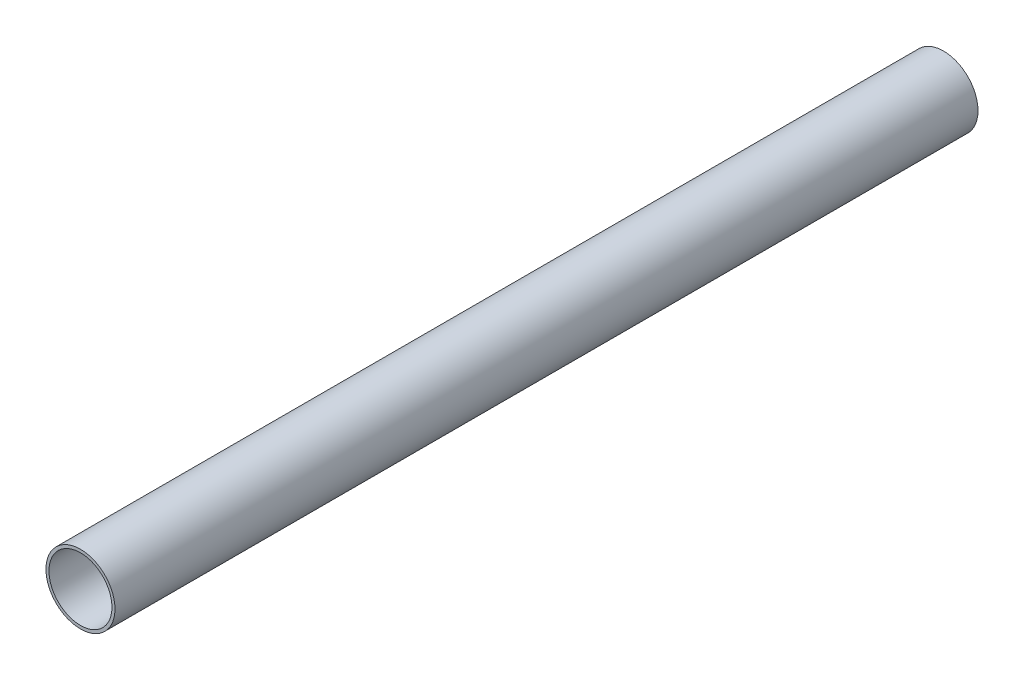
SolidWorks part; units mm, degrees
ref_plane "Plan de face" through (0, 0, 0) normal (0, 0, 1) x (1, 0, 0)
ref_plane "Plan de dessus" through (0, 0, 0) normal (0, 1, 0) x (1, 0, 0)
ref_plane "Plan de droite" through (0, 0, 0) normal (1, 0, 0) x (0, 0, -1)
sketch "Esquisse5" plane through (0, 0, 0) normal (0, 0, 1) x (1, 0, 0)
  circle A0 centre (0, 0) radius 12
  circle A1 centre (0, 0) radius 10.95
extrude "Boss.-Extru.1" add sketch "Esquisse5" along normal blind 300 contours A0 | A1
